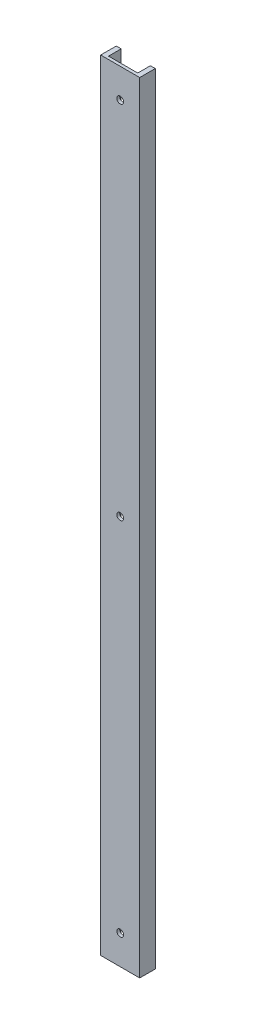
SolidWorks part; units mm, degrees
material "6061-T6 (SS)"
ref_plane "Front Plane" through (0, 0, 0) normal (0, 0, 1) x (1, 0, 0)
ref_plane "Top Plane" through (0, 0, 0) normal (0, 1, 0) x (1, 0, 0)
ref_plane "Right Plane" through (0, 0, 0) normal (1, 0, 0) x (0, 0, -1)
sketch "Sketch1" plane through (0, 0, 0) normal (0, 1, 0) x (1, 0, 0)
  line L1 (0, 0) -> (20, 0)
  line L2 (0, 0) -> (0, 8)
  line L3 (0, 8) -> (20, 8)
  line L4 (20, 0) -> (20, 8)
  dimension "D1" = 20
  dimension "D2" = 8
extrude "Boss-Extrude1" add sketch "Sketch1" along normal blind 400
sketch "Sketch2" plane through (0, 400, 0) normal (0, 1, 0) x (1, 0, 0)
  line L0 (20, 8) -> (0, 8) construction
  line L1 (17.5, 14.5) -> (2.5, 14.5)
  line L2 (17.5, 14.5) -> (17.5, 1.5)
  line L3 (17.5, 1.5) -> (2.5, 1.5)
  line L4 (2.5, 14.5) -> (2.5, 1.5)
  line L5 (17.5, 14.5) -> (2.5, 1.5) construction
  line L6 (17.5, 1.5) -> (2.5, 14.5) construction
  line L7 (0, 8) -> (0, 0) construction
  line L8 (0, 0) -> (20, 0) construction
  point P0 (10, 8)
  dimension "D1" = 2.5
  dimension "D2" = 1.5
extrude "Cut-Extrude1" cut sketch "Sketch2" against normal through all
sketch "Sketch3" plane through (0, 0, -1.5) normal (0, 0, -1) x (-1, 0, 0)
  line L0 (-10, 400) -> (-10, 0) construction
  line L1 (-2.5, 400) -> (-17.5, 400) construction
  line L2 (-2.5, 0) -> (-17.5, 0) construction
  circle A0 centre (-10, 385) radius 1.75
  circle A1 centre (-10, 200) radius 1.75
  circle A2 centre (-10, 15) radius 1.75
  dimension "D3" = 3.5
  dimension "D1" = 15
  dimension "D2" = 15
extrude "Cut-Extrude2" cut sketch "Sketch3" against normal through all
